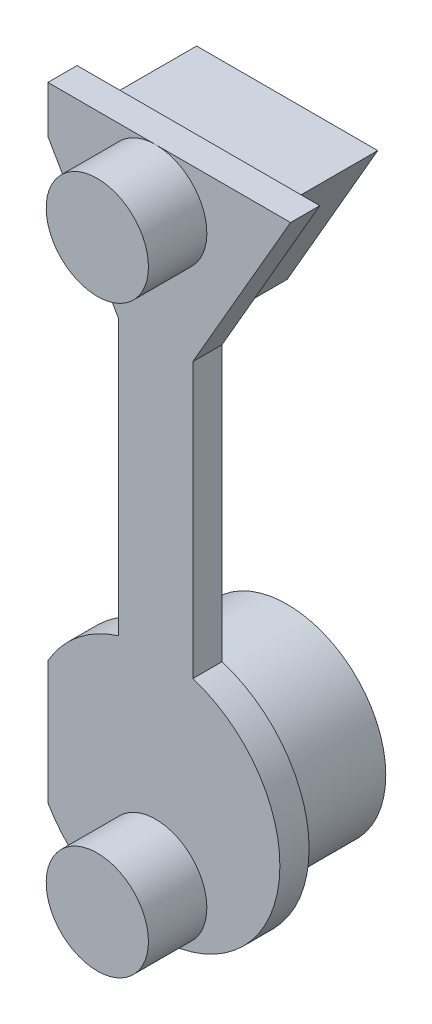
SolidWorks part; units mm, degrees
ref_plane "Спереди" through (0, 0, 0) normal (0, 0, 1) x (1, 0, 0)
ref_plane "Сверху" through (0, 0, 0) normal (0, 1, 0) x (1, 0, 0)
ref_plane "Справа" through (0, 0, 0) normal (1, 0, 0) x (0, 0, -1)
other "Configuration Table"
sketch "Эскиз4" plane through (0, 0, 0) normal (0, 0, 1) x (1, 0, 0)
  line L0 (0.1267, 3.8038) -> (-2.8733, 9)
  line L1 (3.1267, 9) -> (-2.8733, 9)
  line L2 (0.1267, 3.8038) -> (3.1267, 9)
  circle A0 centre (0.1267, -6) radius 3
  arc A1 (-3.1267, 10.4302) -> (-3.1267, 13.5698) centre (-1.3733, 12) ccw
  arc A2 (-3.1267, -13.5698) -> (-3.1267, -10.4302) centre (-1.3733, -12) ccw
  circle A3 centre (0.1267, -8) radius 0.8
  circle A4 centre (0.1267, 8) radius 0.8
sketch "Эскиз5" plane through (0, 0, 0) normal (0, 0, 1) x (1, 0, 0)
  line L0 (-3.5661, 9.4) -> (3.8195, 9.4)
  line L1 (3.8195, 9.4) -> (0.1267, 3.0038)
  line L2 (0.1267, 3.0038) -> (-3.5661, 9.4)
  line L3 (0.1267, 3.8038) -> (3.1267, 9) construction
  line L6 (3.1267, 9) -> (-2.8733, 9) construction
  line L7 (0.1267, 3.8038) -> (-2.8733, 9) construction
  circle A0 centre (0.1267, -6) radius 3.4
  circle A1 centre (0.1267, -6) radius 3 construction
  dimension "D4" = 0.4
  dimension "D1" = 0.4
  dimension "D2" = 0.4
  dimension "D3" = 0.4
extrude "Бобышка-Вытянуть2" add sketch "Эскиз5" along normal blind 0.8
sketch "Эскиз6" plane through (0, 0, 0) normal (0, 0, -1) x (-1, 0, 0)
  line L0 (-0.1267, 3.0038) -> (-3.8195, 9.4) construction
  line L1 (-1.1427, 4.7636) -> (0.8893, 4.7636)
  line L2 (-1.1427, 4.7636) -> (-1.1427, -2.7553)
  line L3 (-1.1427, -2.7553) -> (0.8893, -2.7553)
  line L4 (0.8893, 4.7636) -> (0.8893, -2.7553)
  line L5 (3.5661, 9.4) -> (-0.1267, 3.0038) construction
  circle A0 centre (-0.1267, -6) radius 3.4 construction
  point P8 (0, 0)
  point P11 (0, 0)
  point P12 (0, 0)
extrude "Бобышка-Вытянуть3" add sketch "Эскиз6" against normal blind 0.8
sketch "Эскиз7" plane through (0, 0, 0) normal (0, 0, -1) x (-1, 0, 0)
  line L0 (-2.6071, 8.7) -> (2.3537, 8.7)
  line L1 (2.3537, 8.7) -> (-0.1267, 4.4038)
  line L2 (-0.1267, 4.4038) -> (-2.6071, 8.7)
  line L3 (-3.1267, 9) -> (2.8733, 9) construction
  line L4 (-0.1267, 3.8038) -> (2.8733, 9) construction
  line L5 (-0.1267, 3.8038) -> (-3.1267, 9) construction
  circle A0 centre (-0.1267, -6) radius 2.7
  circle A1 centre (-0.1267, -6) radius 3 construction
  dimension "D4" = 0.3
  dimension "D1" = 0.3
  dimension "D2" = 0.3
  dimension "D3" = 0.3
extrude "Бобышка-Вытянуть4" add sketch "Эскиз7" along normal blind 2.8
sketch "Эскиз8" plane through (0, 0, 0.8) normal (0, 0, 1) x (1, 0, 0)
  circle A0 centre (0.1267, 8) radius 1.4
  circle A1 centre (0.1267, -8) radius 1.4
extrude "Бобышка-Вытянуть5" add sketch "Эскиз8" along normal blind 1.6
sketch "Эскиз9" plane through (0, 0, 0.8) normal (0, 0, 1) x (1, 0, 0)
  line L0 (-3.1267, 10.4302) -> (-3.1267, -10.4302) construction
  line L2 (-7.1065, 11.8338) -> (-2.8267, 11.8338)
  line L3 (-7.1065, 11.8338) -> (-7.1065, -11.4729)
  line L4 (-7.1065, -11.4729) -> (-2.8267, -11.4729)
  line L5 (-2.8267, 11.8338) -> (-2.8267, -11.4729)
  dimension "D1" = 0.3
extrude "Вырез-Вытянуть1" cut sketch "Эскиз9" against normal blind 0.8
